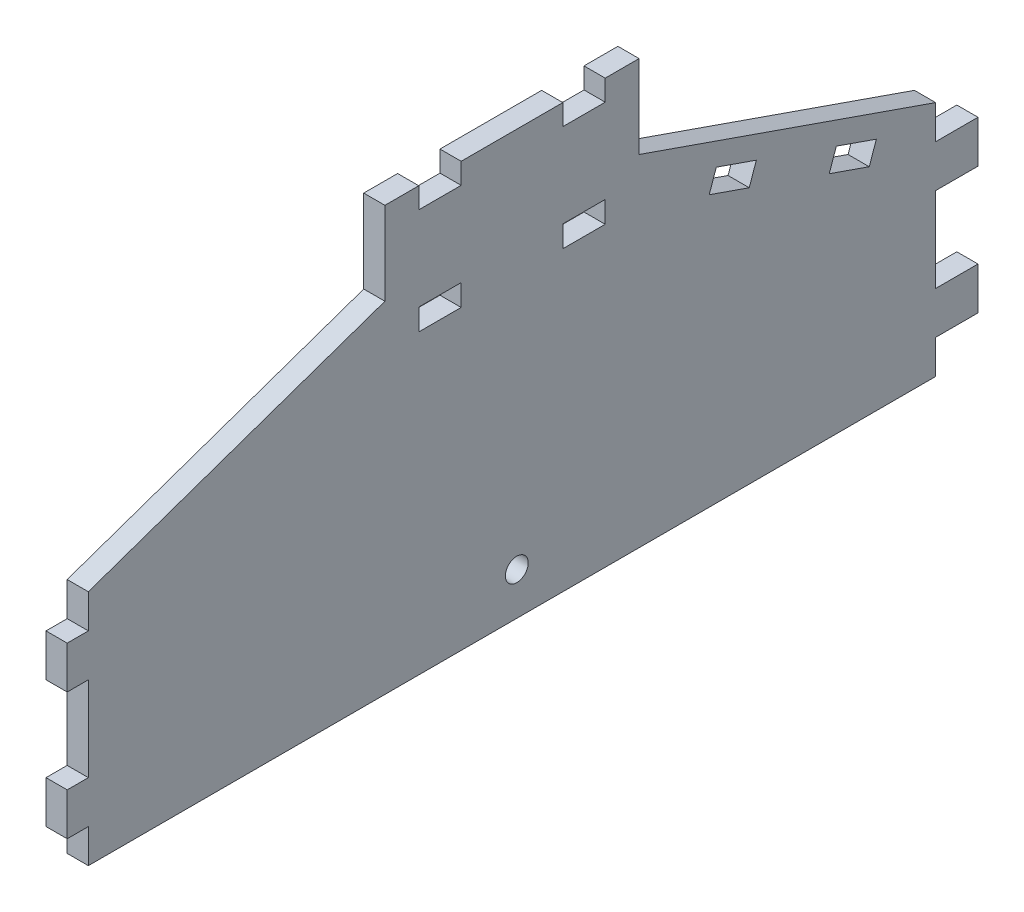
SolidWorks part; units mm, degrees
ref_plane "Front Plane" through (0, 0, 0) normal (0, 0, 1) x (1, 0, 0)
ref_plane "Top Plane" through (0, 0, 0) normal (0, 1, 0) x (1, 0, 0)
ref_plane "Right Plane" through (0, 0, 0) normal (1, 0, 0) x (0, 0, -1)
sketch "Sketch1" plane through (0, 0, 0) normal (1, 0, 0) x (0, 0, -1)
  line L1 (-19.05, -31.75) -> (19.05, -31.75)
  line L2 (-19.05, -31.75) -> (-19.05, 31.75)
  line L3 (-19.05, 31.75) -> (19.05, 31.75)
  line L4 (19.05, -31.75) -> (19.05, 31.75)
  line L5 (-19.05, -31.75) -> (19.05, 31.75) construction
  line L6 (-19.05, 31.75) -> (19.05, -31.75) construction
  point P0 (0, 0)
  dimension "D1" = 38.1
  dimension "D2" = 63.5
extrude "Boss-Extrude1" add sketch "Sketch1" along normal blind 3.175
sketch "Sketch2" plane through (0, 0, 0) normal (-1, 0, 0) x (0, 0, 1)
  line L0 (-13.97, 31.75) -> (-7.62, 31.75)
  line L1 (-13.97, 31.75) -> (-13.97, 28.6258)
  line L2 (-7.62, 31.75) -> (-7.62, 28.6258)
  line L3 (-13.97, 28.6258) -> (-7.62, 28.6258)
  line L4 (-19.05, 31.75) -> (19.05, 31.75) construction
  line L5 (7.62, 31.75) -> (7.62, 28.6258)
  line L6 (7.62, 31.75) -> (13.97, 31.75)
  line L7 (7.62, 28.6258) -> (13.97, 28.6258)
  line L8 (13.97, 31.75) -> (13.97, 28.6258)
  line L9 (0, 31.75) -> (0, 0) construction
  dimension "D1" = 7.62
  dimension "D2" = 7.62
  dimension "D3" = 6.35
  dimension "D4" = 6.35
  dimension "D5" = 3.1242
  dimension "D6" = 3.1242
extrude "Cut-Extrude1" cut sketch "Sketch2" against normal through all
sketch "Sketch3" plane through (0, 0, 0) normal (-1, 0, 0) x (0, 0, 1)
  line L0 (0, 31.75) -> (0, 0) construction
  line L1 (-13.97, 16.002) -> (-7.62, 16.002)
  line L2 (-13.97, 16.002) -> (-13.97, 12.7762)
  line L3 (-13.97, 12.7762) -> (-7.62, 12.7762)
  line L4 (-7.62, 16.002) -> (-7.62, 12.7762)
  line L5 (-13.97, 16.002) -> (-7.62, 12.7762) construction
  line L6 (-13.97, 12.7762) -> (-7.62, 16.002) construction
  line L7 (7.62, 16.002) -> (13.97, 16.002)
  line L8 (7.62, 16.002) -> (7.62, 12.7762)
  line L9 (7.62, 12.7762) -> (13.97, 12.7762)
  line L10 (13.97, 16.002) -> (13.97, 12.7762)
  line L11 (7.62, 16.002) -> (13.97, 12.7762) construction
  line L12 (7.62, 12.7762) -> (13.97, 16.002) construction
  line L13 (-7.62, 31.75) -> (7.62, 31.75) construction
  line L14 (-7.62, 14.3891) -> (7.62, 14.3891) construction
  point P0 (-10.795, 14.3891)
  point P5 (10.795, 14.3891)
  dimension "D1" = 6.35
  dimension "D2" = 6.35
  dimension "D3" = 3.2258
  dimension "D4" = 3.2258
  dimension "D5" = 7.62
  dimension "D6" = 7.62
  dimension "D7" = 15.748
extrude "cut for tabs servo plate" cut sketch "Sketch3" against normal through all
sketch "Sketch4" plane through (0, 0, 0) normal (-1, 0, 0) x (0, 0, 1)
  line L0 (19.05, -31.75) -> (63.5, -31.75)
  line L1 (63.5, -31.75) -> (63.5, 3.81)
  line L2 (63.5, 3.81) -> (19.05, 19.2956)
  line L3 (19.05, 31.75) -> (19.05, -31.75) construction
  line L4 (19.05, 19.2956) -> (19.05, -31.75)
  dimension "D1" = 35.56
  dimension "D2" = 44.45
extrude "base extension" add sketch "Sketch4" against normal blind 3.175
mirror "Mirror1" about plane through (0, 0, 0) normal (0, 0, 1) of "base extension"
sketch "Sketch5" plane through (3.175, 0, 0) normal (1, 0, 0) x (0, 0, -1)
  line L0 (63.5, -1.27) -> (63.5, -7.62)
  line L1 (63.5, -1.27) -> (69.85, -1.27)
  line L2 (63.5, -7.62) -> (69.85, -7.62)
  line L3 (69.85, -1.27) -> (69.85, -7.62)
  line L4 (63.5, -31.75) -> (63.5, 3.81) construction
  line L5 (63.5, -20.32) -> (63.5, -26.67)
  line L6 (63.5, -20.32) -> (69.85, -20.32)
  line L7 (63.5, -26.67) -> (69.85, -26.67)
  line L8 (69.85, -20.32) -> (69.85, -26.67)
  line L9 (63.5, -13.97) -> (-63.6861, -13.97) construction
  line L10 (-63.5, -1.27) -> (-63.5, -7.62)
  line L11 (-63.5, -1.27) -> (-66.675, -1.27)
  line L12 (-63.5, -7.62) -> (-66.675, -7.62)
  line L13 (-66.675, -1.27) -> (-66.675, -7.62)
  line L14 (-63.5, -31.75) -> (-63.5, 3.81) construction
  line L15 (-63.5, -20.32) -> (-63.5, -26.67)
  line L16 (-63.5, -20.32) -> (-66.675, -20.32)
  line L17 (-63.5, -26.67) -> (-66.675, -26.67)
  line L18 (-66.675, -20.32) -> (-66.675, -26.67)
  dimension "D1" = 6.35
  dimension "D2" = 6.35
  dimension "D3" = 6.35
  dimension "D4" = 6.35
  dimension "D5" = 6.35
  dimension "D6" = 6.35
  dimension "D7" = 3.175
  dimension "D8" = 6.35
  dimension "D9" = 6.35
  dimension "D10" = 3.175
  dimension "D11" = 6.35
  dimension "D12" = 6.35
extrude "tabs" add sketch "Sketch5" against normal blind 3.175
sketch "Sketch6" plane through (0, 0, 0) normal (-1, 0, 0) x (0, 0, 1)
  line L0 (-59.8483, 1.6797) -> (-23.1407, 14.468) construction
  line L1 (-63.5, 3.81) -> (-19.05, 19.2956) construction
  line L2 (-36.6204, 9.7719) -> (-30.6239, 11.8609)
  line L3 (-30.6239, 11.8609) -> (-29.5627, 8.8147)
  line L4 (-29.5627, 8.8147) -> (-35.5592, 6.7256)
  line L5 (-35.5592, 6.7256) -> (-36.6204, 9.7719)
  line L6 (-48.6135, 5.5937) -> (-47.5522, 2.5475)
  line L7 (-47.5522, 2.5475) -> (-53.5487, 0.4584)
  line L8 (-53.5487, 0.4584) -> (-54.61, 3.5046)
  line L9 (-54.61, 3.5046) -> (-48.6135, 5.5937)
  dimension "D1" = 3.2258
  dimension "D2" = 3.2258
  dimension "D3" = 3.2131
  dimension "D4" = 6.35
  dimension "D5" = 6.35
  dimension "D6" = 12.7
  dimension "D7" = 8.89
extrude "cut for neck cover tabs" cut sketch "Sketch6" against normal through all
sketch "Sketch7" plane through (0, 0, 0) normal (-1, 0, 0) x (0, 0, 1)
  circle A0 centre (-0.718, -25.4) radius 1.7145
  dimension "D1" = 3.429
extrude "Cut-Extrude2" cut sketch "Sketch7" against normal through all
